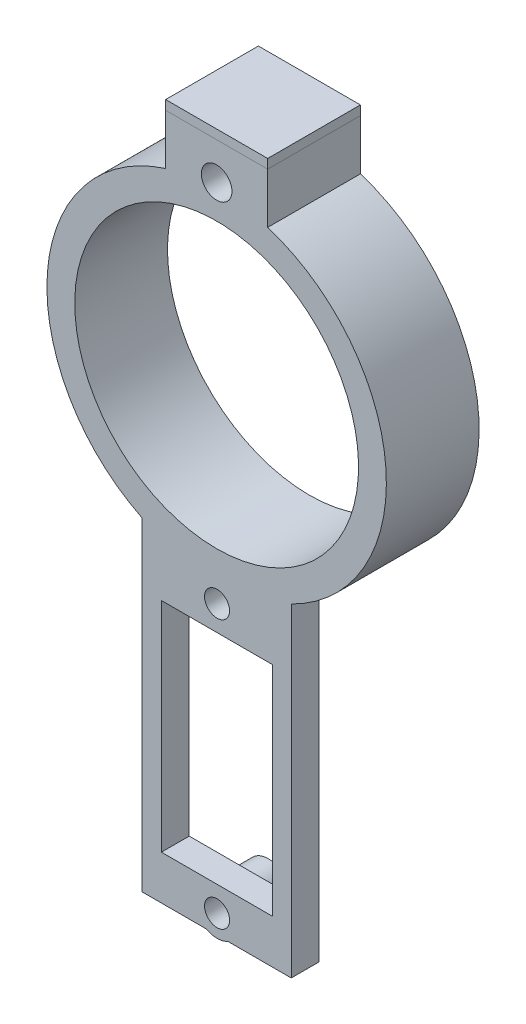
SolidWorks part; units mm, degrees
ref_plane "Front Plane" through (0, 0, 0) normal (0, 0, 1) x (1, 0, 0)
ref_plane "Top Plane" through (0, 0, 0) normal (0, 1, 0) x (1, 0, 0)
ref_plane "Right Plane" through (0, 0, 0) normal (1, 0, 0) x (0, 0, -1)
sketch "Sketch2" plane through (0, 0, 0) normal (0, 0, 1) x (1, 0, 0)
  circle A0 centre (0, 0) radius 15.3
  circle A1 centre (0, 0) radius 18.3
  dimension "D1" = 3
  dimension "D2" = 30.6
extrude "Extrude1" add sketch "Sketch2" along normal blind 10
sketch "Sketch3" plane through (0, 0, 10) normal (0, 0, 1) x (1, 0, 0)
  line L0 (-8.044, -16.4373) -> (8.044, -16.4373)
  line L1 (-8.044, -16.4373) -> (-8.044, -51.3631)
  line L2 (-8.044, -51.3631) -> (8.044, -51.3631)
  line L3 (8.044, -51.3631) -> (8.044, -16.4373)
  line L7 (-5.956, -23.1131) -> (6.044, -23.1131)
  line L8 (-5.956, -23.1131) -> (-5.956, -46.6131)
  line L9 (-5.956, -46.6131) -> (6.044, -46.6131)
  line L10 (6.044, -23.1131) -> (6.044, -46.6131)
  circle A0 centre (0, 0) radius 18.3 construction
  dimension "D1" = 12
  dimension "D4" = 2
  dimension "D2" = 23.5
  dimension "D3" = 4.75
extrude "Extrude2" add sketch "Sketch3" against normal blind 3
sketch "Sketch4" plane through (0, 0, 0) normal (0, 0, -1) x (-1, 0, 0)
  line L0 (0, -51.3631) -> (0, 18.3) construction
  line L1 (8.044, -51.3631) -> (-8.044, -51.3631) construction
  line L2 (-3.5, 18.3) -> (3.5, 18.3)
  line L3 (-3.5, 18.3) -> (-3.5, 14.8943)
  line L4 (3.5, 18.3) -> (3.5, 14.8943)
  line L5 (3.5, 14.8943) -> (-3.5, 14.8943)
  circle A0 centre (0, 0) radius 18.3 construction
  circle A1 centre (0, 0) radius 15.3 construction
  point P9 (0, 18.3)
  dimension "D1" = 7
extrude "Extrude3" cut sketch "Sketch4" against normal through all
sketch "Sketch5" plane through (0, 0, 0) normal (0, 0, -1) x (-1, 0, 0)
  line L0 (-3.5, 14.8943) -> (3.5, 14.8943)
  line L1 (3.5, 14.8943) -> (3.5, 22.8943)
  line L2 (3.5, 22.8943) -> (-3.5, 22.8943)
  line L3 (-3.5, 22.8943) -> (-3.5, 14.8943)
  dimension "D1" = 8
extrude "Extrude4" add sketch "Sketch5" against normal up to surface (10 mm away) separate body up to face at (0, -12.1017, 10)
sketch "Sketch6" plane through (-3.5, 0, 0) normal (-1, 0, 0) x (0, 0, 1)
  line L0 (10, 14.8943) -> (0, 22.8943)
  line L2 (10, 14.8943) -> (0, 14.8943)
  line L4 (0, 22.8943) -> (0, 14.8943)
extrude "Extrude5" cut sketch "Sketch6" against normal up to surface (7 mm away) up to face at (3.5, 18.8943, 5)
sketch "Sketch7" plane through (-3.5, 0, 0) normal (-1, 0, 0) x (0, 0, 1)
  line L1 (0, 22.8943) -> (10, 22.8943)
  line L2 (0, 22.8943) -> (0, 14.8943)
  line L3 (0, 14.8943) -> (10, 14.8943)
  line L4 (10, 22.8943) -> (10, 14.8943)
extrude "Extrude6" add sketch "Sketch7" along normal blind 2
sketch "Sketch8" plane through (3.5, 0, 0) normal (1, 0, 0) x (0, 0, -1)
  line L1 (0, 22.8943) -> (-10, 22.8943)
  line L2 (0, 22.8943) -> (0, 14.8943)
  line L3 (0, 14.8943) -> (-10, 14.8943)
  line L4 (-10, 22.8943) -> (-10, 14.8943)
extrude "Extrude7" add sketch "Sketch8" along normal blind 2
sketch "Sketch9" plane through (0, 22.8943, 0) normal (0, 1, 0) x (1, 0, 0)
  line L1 (5.5, -10) -> (-5.5, -10)
  line L2 (5.5, -10) -> (5.5, 0)
  line L3 (5.5, 0) -> (-5.5, 0)
  line L4 (-5.5, -10) -> (-5.5, 0)
extrude "Extrude9" add sketch "Sketch9" along normal blind 1 separate body
sketch "Sketch10" plane through (0, 0, 10) normal (0, 0, 1) x (1, 0, 0)
  line L0 (-5.5, 22.8943) -> (5.5, 22.8943) construction
  line L1 (-3.5, 14.8943) -> (3.5, 14.8943) construction
  line L2 (-3.5, 14.8943) -> (-3.5, 22.8943) construction
  line L3 (-3.5, 22.8943) -> (3.5, 22.8943) construction
  line L4 (3.5, 14.8943) -> (3.5, 22.8943) construction
  line L5 (-3.5, 22.8943) -> (3.5, 14.8943) construction
  line L6 (3.5, 22.8943) -> (-3.5, 14.8943) construction
  circle A0 centre (0, 18.8943) radius 1.65
extrude "Extrude10" cut sketch "Sketch10" against normal blind 4.2
sketch "Sketch11" plane through (0, 0, 5.8) normal (0, 0, 1) x (1, 0, 0)
  circle A0 centre (0, 18.8943) radius 1.15
extrude "Extrude12" cut sketch "Sketch11" against normal through all
sketch "Sketch12" plane through (0, 0, 0) normal (0, 0, -1) x (-1, 0, 0)
  circle A0 centre (0, 0) radius 15.3
  arc A2 (-3.5, 14.8943) -> (3.5, 14.8943) centre (0, 0) ccw construction
extrude "Extrude13" cut sketch "Sketch12" against normal through all
sketch "Sketch29" plane through (0, 0, 10) normal (0, 0, 1) x (1, 0, 0)
  line L0 (-5.956, -46.6131) -> (6.044, -46.6131) construction
  line L1 (0.044, -46.6131) -> (0.0465, -49.3131) construction
  line L2 (6.044, -23.1131) -> (-5.956, -23.1131) construction
  line L3 (0.044, -23.1131) -> (0.044, -20.4131) construction
  circle A0 centre (0.044, -20.4131) radius 2.35
  circle A1 centre (0.0465, -49.3131) radius 2.35
  dimension "D1" = 2.7
extrude "Extrude30" add sketch "Sketch29" against normal blind 5.5
sketch "Sketch31" plane through (0, 0, 10) normal (0, 0, 1) x (1, 0, 0)
  circle A0 centre (0.0465, -49.3131) radius 1.35
  circle A1 centre (0.044, -20.4131) radius 1.35
extrude "Extrude31" cut sketch "Sketch31" against normal blind 3.5
